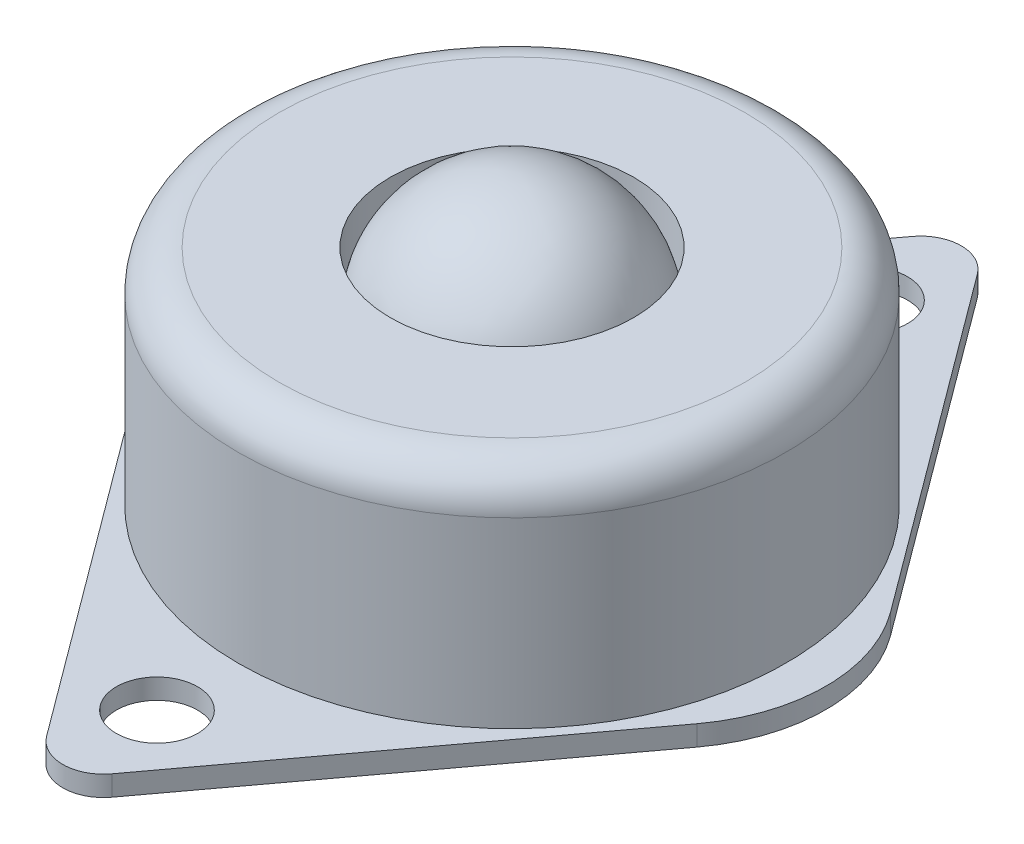
SolidWorks part; units mm, degrees
ref_plane "前视基准面" through (0, 0, 0) normal (0, 0, 1) x (1, 0, 0)
ref_plane "上视基准面" through (0, 0, 0) normal (0, 1, 0) x (1, 0, 0)
ref_plane "右视基准面" through (0, 0, 0) normal (1, 0, 0) x (0, 0, -1)
sketch "草图1" plane through (0, 0, 0) normal (0, 1, 0) x (1, 0, 0)
  line L0 (0, 28.2203) -> (0, -28.2203) construction
  line L1 (-22.7733, 0) -> (38.1873, 0) construction
  line L2 (-1.6063, 21.3343) -> (-13.8958, 4.766)
  line L3 (-13.8958, -4.766) -> (-1.6063, -21.3343)
  line L4 (13.8958, -4.766) -> (1.6063, -21.3343)
  line L5 (1.6063, 21.3343) -> (13.8958, 4.766)
  circle A0 centre (0, 0) radius 14
  circle A1 centre (0, 17.5) radius 2
  circle A2 centre (0, -17.5) radius 2
  arc A3 (1.6063, 21.3343) -> (-1.6063, 21.3343) centre (0, 20.1429) ccw
  arc A4 (-1.6063, -21.3343) -> (1.6063, -21.3343) centre (0, -20.1429) ccw
  arc A5 (-13.8958, 4.766) -> (-13.8958, -4.766) centre (-7.4704, 0) ccw
  arc A6 (13.8958, -4.766) -> (13.8958, 4.766) centre (7.4704, 0) ccw
  point P17 (0, 23.5)
  point P20 (0, -23.5)
  point P23 (-17.4308, 0)
  point P26 (17.4308, 0)
  dimension "D1" = 28
  dimension "D2" = 4
  dimension "D3" = 35
  dimension "D5" = 2
  dimension "D6" = 2
  dimension "D7" = 8
  dimension "D8" = 8
  dimension "D4" = 47
extrude "凸台-拉伸1" add sketch "草图1" along normal blind 1 contours L5 A3 L2 A0 A1 | A0 | L4 A6 L5 A0 | L3 A4 L4 A0 A2 | L2 A5 L3 A0
sketch "草图2" plane through (0, 1, 0) normal (0, 1, 0) x (1, 0, 0)
  line L4 (13.8958, 4.766) -> (1.6063, 21.3343)
  line L5 (-1.6063, 21.3343) -> (-13.8958, 4.766)
  line L6 (-13.8958, -4.766) -> (-1.6063, -21.3343)
  line L7 (1.6063, -21.3343) -> (13.8958, -4.766)
  line L8 (13.8958, 4.766) -> (1.6063, 21.3343)
  line L9 (-1.6063, 21.3343) -> (-13.8958, 4.766)
  line L10 (-13.8958, -4.766) -> (-1.6063, -21.3343)
  line L11 (1.6063, -21.3343) -> (13.8958, -4.766)
  circle A0 centre (0, 0) radius 13.5
  circle A1 centre (0, 0) radius 6
  arc A4 (1.6063, 21.3343) -> (-1.6063, 21.3343) centre (0, 20.1429) ccw
  arc A5 (-13.8958, 4.766) -> (-13.8958, -4.766) centre (-7.4704, 0) ccw
  arc A6 (-1.6063, -21.3343) -> (1.6063, -21.3343) centre (0, -20.1429) ccw
  arc A7 (13.8958, -4.766) -> (13.8958, 4.766) centre (7.4704, 0) ccw
  arc A8 (1.6063, 21.3343) -> (-1.6063, 21.3343) centre (0, 20.1429) ccw
  arc A9 (-13.8958, 4.766) -> (-13.8958, -4.766) centre (-7.4704, 0) ccw
  arc A10 (-1.6063, -21.3343) -> (1.6063, -21.3343) centre (0, -20.1429) ccw
  arc A11 (13.8958, -4.766) -> (13.8958, 4.766) centre (7.4704, 0) ccw
  dimension "D2" = 27
  dimension "D3" = 12
  dimension "D1" = 0
extrude "凸台-拉伸2" add sketch "草图2" along normal blind 11 contours A0
fillet "圆角1" radius 2 1 edges at (0, 12, 13.5)
ref_plane "基准面1" through (0, 9, 0) normal (0, 1, 0) x (1, 0, 0)
sketch "草图5" plane through (0, 9, 0) normal (0, 1, 0) x (1, 0, 0)
  line L0 (6, 0) -> (-6, 0)
  circle A0 centre (0, 0) radius 6
  circle A1 centre (0, 0) radius 6
  circle A2 centre (0, 0) radius 6
  dimension "D1" = 0
revolve "旋转3" add sketch "草图5" angle 360 about L0
